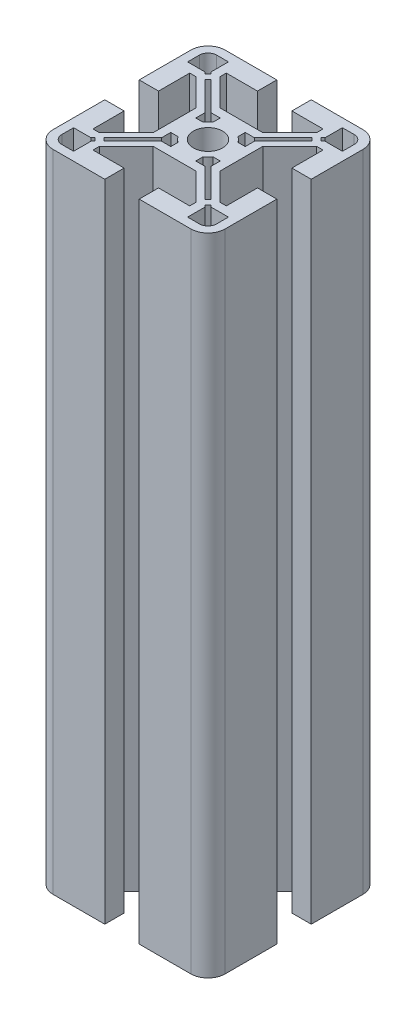
SolidWorks part; units mm, degrees
ref_plane "Ebene vorne" through (0, 0, 0) normal (0, 0, 1) x (1, 0, 0)
ref_plane "Ebene oben" through (0, 0, 0) normal (0, 1, 0) x (1, 0, 0)
ref_plane "Ebene rechts" through (0, 0, 0) normal (1, 0, 0) x (0, 0, -1)
sketch "Sketch1" plane through (0, 0, 0) normal (0, 1, 0) x (1, 0, 0)
  line L0 (-7.9326, -10.8599) -> (-58.869, -10.8599) construction
  line L1 (-7.9326, -10.8599) -> (-7.9326, 43.7859) construction
  line L2 (-7.9326, -10.8599) -> (-62.5783, 43.7859) construction
  line L3 (-27.9326, -6.8599) -> (-27.9326, 5.1401)
  line L4 (-27.9326, -6.8599) -> (-23.4326, -6.8599)
  line L5 (-23.4326, -6.8599) -> (-23.4326, 0.3901)
  line L6 (-23.4326, 0.3901) -> (-21.9326, 0.3901)
  line L7 (-21.9326, 0.3901) -> (-15.6826, -5.8599)
  line L8 (-15.6826, -5.8599) -> (-15.6826, -10.8599)
  line L9 (-25.9326, 2.3901) -> (-25.9326, 5.1401)
  line L10 (-25.9326, 2.3901) -> (-21.8897, 2.3901)
  line L11 (-21.4415, 1.9419) -> (-20.7344, 2.649)
  line L12 (-21.4415, 1.9419) -> (-21.8897, 2.3901)
  line L13 (-20.3808, 0.8813) -> (-13.6826, -5.817)
  line L14 (-13.6826, -5.817) -> (-13.6826, -7.9551)
  line L15 (-20.3808, 0.8813) -> (-19.6737, 1.5884)
  line L16 (-13.6826, -7.9551) -> (-13.1826, -7.9551)
  line L17 (-19.6737, 1.5884) -> (-12.9755, -5.1099)
  line L18 (-10.8374, -5.1099) -> (-10.8374, -5.6099)
  line L19 (-12.9755, -5.1099) -> (-10.8374, -5.1099)
  line L20 (-21.1826, 7.1401) -> (-21.1826, 3.0973)
  line L21 (-21.1826, 7.1401) -> (-23.9326, 7.1401)
  line L22 (-19.1826, 3.1401) -> (-12.9326, -3.1099)
  line L23 (-11.9326, 9.1401) -> (-11.9326, 4.6401)
  line L24 (-19.1826, 4.6401) -> (-19.1826, 3.1401)
  line L25 (-12.9326, -3.1099) -> (-7.9326, -3.1099)
  line L26 (-11.9326, 4.6401) -> (-19.1826, 4.6401)
  line L27 (-11.9326, 9.1401) -> (-23.9326, 9.1401)
  line L28 (7.5674, -6.8599) -> (7.5674, 0.3901)
  line L29 (12.0674, -6.8599) -> (12.0674, 5.1401)
  line L30 (12.0674, -6.8599) -> (7.5674, -6.8599)
  line L31 (10.0674, 2.3901) -> (10.0674, 5.1401)
  line L32 (10.0674, 2.3901) -> (6.0245, 2.3901)
  line L33 (6.0674, 0.3901) -> (-0.1826, -5.8599)
  line L34 (7.5674, 0.3901) -> (6.0674, 0.3901)
  line L35 (-0.1826, -5.8599) -> (-0.1826, -10.8599)
  line L36 (-2.1826, -5.817) -> (-2.1826, -7.9551)
  line L37 (3.8085, 1.5884) -> (-2.8897, -5.1099)
  line L38 (4.5156, 0.8813) -> (-2.1826, -5.817)
  line L39 (-2.8897, -5.1099) -> (-5.0279, -5.1099)
  line L40 (-5.0279, -5.1099) -> (-5.0279, -5.6099)
  line L41 (-2.1826, -7.9551) -> (-2.6826, -7.9551)
  line L42 (-2.9326, -3.1099) -> (-7.9326, -3.1099)
  line L43 (3.3174, 3.1401) -> (-2.9326, -3.1099)
  line L44 (5.3174, 7.1401) -> (5.3174, 3.0973)
  line L45 (5.3174, 7.1401) -> (8.0674, 7.1401)
  line L46 (-3.9326, 4.6401) -> (3.3174, 4.6401)
  line L47 (3.3174, 4.6401) -> (3.3174, 3.1401)
  line L48 (-3.9326, 9.1401) -> (8.0674, 9.1401)
  line L49 (-3.9326, 9.1401) -> (-3.9326, 4.6401)
  line L50 (-3.9326, -26.3599) -> (3.3174, -26.3599)
  line L51 (-3.9326, -30.8599) -> (8.0674, -30.8599)
  line L52 (-3.9326, -30.8599) -> (-3.9326, -26.3599)
  line L53 (5.3174, -28.8599) -> (8.0674, -28.8599)
  line L54 (5.3174, -28.8599) -> (5.3174, -24.817)
  line L55 (3.3174, -24.8599) -> (-2.9326, -18.6099)
  line L56 (3.3174, -26.3599) -> (3.3174, -24.8599)
  line L57 (-2.9326, -18.6099) -> (-7.9326, -18.6099)
  line L58 (-2.8897, -16.6099) -> (-5.0279, -16.6099)
  line L59 (4.5156, -22.601) -> (-2.1826, -15.9027)
  line L60 (3.8085, -23.3081) -> (-2.8897, -16.6099)
  line L61 (-2.1826, -15.9027) -> (-2.1826, -13.7646)
  line L62 (-2.1826, -13.7646) -> (-2.6826, -13.7646)
  line L63 (-5.0279, -16.6099) -> (-5.0279, -16.1099)
  line L64 (-0.1826, -15.8599) -> (-0.1826, -10.8599)
  line L65 (6.0674, -22.1099) -> (-0.1826, -15.8599)
  line L66 (10.0674, -24.1099) -> (6.0245, -24.1099)
  line L67 (10.0674, -24.1099) -> (10.0674, -26.8599)
  line L68 (7.5674, -14.8599) -> (7.5674, -22.1099)
  line L69 (7.5674, -22.1099) -> (6.0674, -22.1099)
  line L70 (12.0674, -14.8599) -> (12.0674, -26.8599)
  line L71 (12.0674, -14.8599) -> (7.5674, -14.8599)
  line L72 (-23.4326, -14.8599) -> (-23.4326, -22.1099)
  line L73 (-27.9326, -14.8599) -> (-27.9326, -26.8599)
  line L74 (-27.9326, -14.8599) -> (-23.4326, -14.8599)
  line L75 (-25.9326, -24.1099) -> (-25.9326, -26.8599)
  line L76 (-25.9326, -24.1099) -> (-21.8897, -24.1099)
  line L77 (-21.9326, -22.1099) -> (-15.6826, -15.8599)
  line L78 (-23.4326, -22.1099) -> (-21.9326, -22.1099)
  line L79 (-15.6826, -15.8599) -> (-15.6826, -10.8599)
  line L80 (-13.6826, -15.9027) -> (-13.6826, -13.7646)
  line L81 (-19.6737, -23.3081) -> (-12.9755, -16.6099)
  line L82 (-20.3808, -22.601) -> (-13.6826, -15.9027)
  line L83 (-12.9755, -16.6099) -> (-10.8374, -16.6099)
  line L84 (-10.8374, -16.6099) -> (-10.8374, -16.1099)
  line L85 (-13.6826, -13.7646) -> (-13.1826, -13.7646)
  line L86 (-12.9326, -18.6099) -> (-7.9326, -18.6099)
  line L87 (-19.1826, -24.8599) -> (-12.9326, -18.6099)
  line L88 (-21.1826, -28.8599) -> (-21.1826, -24.817)
  line L89 (-21.1826, -28.8599) -> (-23.9326, -28.8599)
  line L90 (-11.9326, -26.3599) -> (-19.1826, -26.3599)
  line L91 (-19.1826, -26.3599) -> (-19.1826, -24.8599)
  line L92 (-11.9326, -30.8599) -> (-23.9326, -30.8599)
  line L93 (-11.9326, -30.8599) -> (-11.9326, -26.3599)
  line L94 (-20.7344, 2.649) -> (-21.1826, 3.0973)
  line L95 (4.8692, 2.649) -> (5.3174, 3.0973)
  line L96 (4.8692, 2.649) -> (5.5763, 1.9419)
  line L97 (5.5763, 1.9419) -> (6.0245, 2.3901)
  line L98 (3.8085, 1.5884) -> (4.5156, 0.8813)
  line L99 (5.5763, -23.6616) -> (6.0245, -24.1099)
  line L100 (5.5763, -23.6616) -> (4.8692, -24.3687)
  line L101 (4.8692, -24.3687) -> (5.3174, -24.817)
  line L102 (4.5156, -22.601) -> (3.8085, -23.3081)
  line L103 (-20.7344, -24.3687) -> (-21.1826, -24.817)
  line L104 (-20.7344, -24.3687) -> (-21.4415, -23.6616)
  line L105 (-21.4415, -23.6616) -> (-21.8897, -24.1099)
  line L106 (-19.6737, -23.3081) -> (-20.3808, -22.601)
  line L107 (-13.1826, -7.9551) -> (-12.0023, -7.9551)
  line L108 (-10.8374, -5.6099) -> (-10.8374, -6.7901)
  line L109 (-5.0279, -5.6099) -> (-5.0279, -6.7901)
  line L110 (-2.6826, -7.9551) -> (-3.8629, -7.9551)
  line L111 (-2.6826, -13.7646) -> (-3.8629, -13.7646)
  line L112 (-5.0279, -16.1099) -> (-5.0279, -14.9296)
  line L113 (-10.8374, -16.1099) -> (-10.8374, -14.9296)
  line L114 (-13.1826, -13.7646) -> (-12.0023, -13.7646)
  arc A0 (-27.9326, 5.1401) -> (-23.9326, 9.1401) centre (-23.9326, 5.1401) cw
  arc A1 (-25.9326, 5.1401) -> (-23.9326, 7.1401) centre (-23.9326, 5.1401) cw
  arc A2 (-11.3326, -10.8599) -> (-7.9326, -7.4599) centre (-7.9326, -10.8599) cw
  arc A3 (-12.0023, -13.7646) -> (-10.8374, -14.9296) centre (-7.9326, -10.8599) ccw
  arc A4 (8.0674, 9.1401) -> (12.0674, 5.1401) centre (8.0674, 5.1401) cw
  arc A5 (8.0674, 7.1401) -> (10.0674, 5.1401) centre (8.0674, 5.1401) cw
  arc A6 (-5.0279, -14.9296) -> (-3.8629, -13.7646) centre (-7.9326, -10.8599) ccw
  arc A7 (-7.9326, -7.4599) -> (-4.5326, -10.8599) centre (-7.9326, -10.8599) cw
  arc A8 (12.0674, -26.8599) -> (8.0674, -30.8599) centre (8.0674, -26.8599) cw
  arc A9 (10.0674, -26.8599) -> (8.0674, -28.8599) centre (8.0674, -26.8599) cw
  arc A10 (-3.8629, -7.9551) -> (-5.0279, -6.7901) centre (-7.9326, -10.8599) ccw
  arc A11 (-4.5326, -10.8599) -> (-7.9326, -14.2599) centre (-7.9326, -10.8599) cw
  arc A12 (-23.9326, -30.8599) -> (-27.9326, -26.8599) centre (-23.9326, -26.8599) cw
  arc A13 (-23.9326, -28.8599) -> (-25.9326, -26.8599) centre (-23.9326, -26.8599) cw
  arc A14 (-10.8374, -6.7901) -> (-12.0023, -7.9551) centre (-7.9326, -10.8599) ccw
  arc A15 (-7.9326, -14.2599) -> (-11.3326, -10.8599) centre (-7.9326, -10.8599) cw
  point P19 (-20.0273, 1.2348)
  point P41 (-21.0879, 2.2955)
  point P140 (-7.9326, -10.8599)
  point P149 (-7.9326, -10.8599)
  point P152 (-7.9326, -10.8599)
extrude "Boss-Extrude1" add sketch "Sketch1" along normal mid plane 150 contours A12 L92 L93 L90 L91 L87 L86 L57 L55 L56 L50 L52 L51 A8 L70 L71 L68 L69 L65 L64 L35 L33 L34 L28 L30 L29 A4 L48 L49 L46 L47 L43 L42 L25 L22 L24 L26 L23 L27 A0 L3 L4 L5 L6 L7 L8 L79 L77 L78 L72 L74
